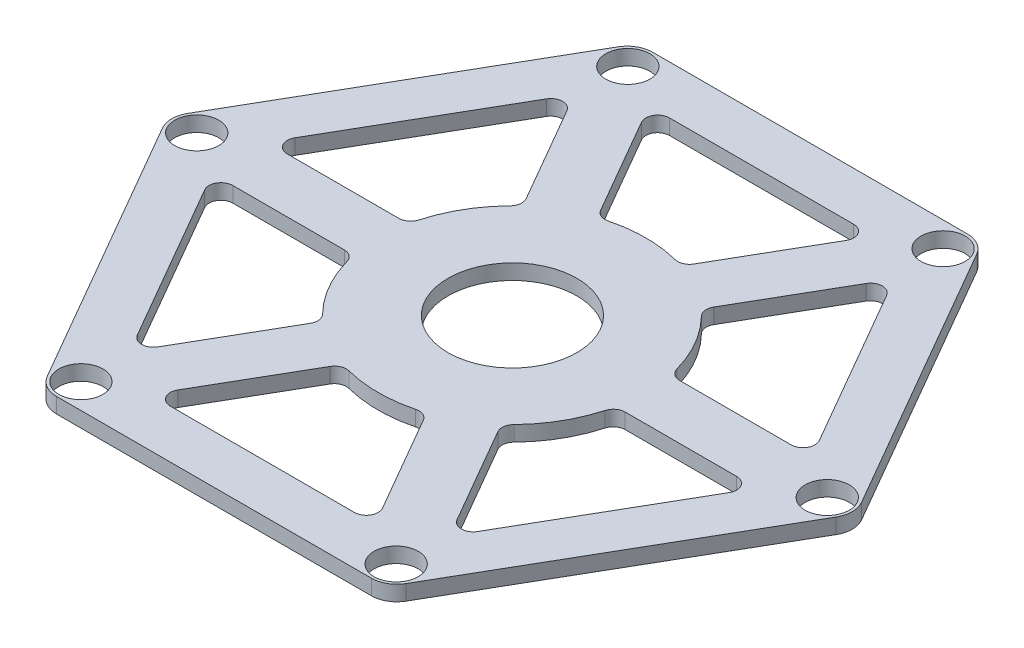
SolidWorks part; units mm, degrees
ref_plane "Front Plane" through (0, 0, 0) normal (0, 0, 1) x (1, 0, 0)
ref_plane "Top Plane" through (0, 0, 0) normal (0, 1, 0) x (1, 0, 0)
ref_plane "Right Plane" through (0, 0, 0) normal (1, 0, 0) x (0, 0, -1)
sketch "Sketch1" plane through (0, 0, 0) normal (0, 1, 0) x (1, 0, 0)
  line L1 (-20.3, 35.1606) -> (-40.6, 0)
  line L2 (-40.6, 0) -> (-20.3, -35.1606)
  line L3 (-20.3, -35.1606) -> (20.3, -35.1606)
  line L4 (20.3, -35.1606) -> (40.6, 0)
  line L5 (40.6, 0) -> (20.3, 35.1606)
  line L6 (20.3, 35.1606) -> (-20.3, 35.1606)
  line L7 (-17, 29.4449) -> (-34, 0)
  line L8 (-34, 0) -> (-17, -29.4449)
  line L9 (-17, -29.4449) -> (17, -29.4449)
  line L10 (17, -29.4449) -> (34, 0)
  line L11 (34, 0) -> (17, 29.4449)
  line L12 (17, 29.4449) -> (-17, 29.4449)
  line L13 (-18.6638, 32.2165) -> (-37.3656, -0.0563) construction
  line L14 (-37.3656, -0.0563) -> (-18.7674, -32.3889) construction
  line L15 (-18.7674, -32.3889) -> (18.5325, -32.4487) construction
  line L16 (18.5325, -32.4487) -> (37.3, 0) construction
  line L17 (37.3, 0) -> (18.6362, 32.2165) construction
  line L18 (18.6362, 32.2165) -> (-18.6638, 32.2165) construction
  line L50 (-17, 29.4449) -> (17, -29.4449) construction
  line L51 (-17, 29.4449) -> (-18.8579, 26.2268)
  line L56 (-13.2841, 29.4449) -> (-17, 29.4449)
  line L57 (-13.3543, 16.6943) -> (-7.7805, 19.9123) construction
  line L58 (-17, 29.4449) -> (-13.2841, 29.4449)
  line L59 (-13.2841, 29.4449) -> (-4.9475, 15.0054)
  line L60 (-17, 29.4449) -> (-18.8579, 26.2268)
  line L61 (-18.8579, 26.2268) -> (-10.5213, 11.7874)
  line L62 (17, 29.4449) -> (13.2841, 29.4449)
  line L63 (13.2841, 29.4449) -> (4.9475, 15.0054)
  line L66 (18.8579, 26.2268) -> (10.5213, 11.7874)
  line L67 (17, 29.4449) -> (18.8579, 26.2268)
  line L68 (34, 0) -> (32.1421, 3.2181)
  line L69 (32.1421, 3.2181) -> (15.4688, 3.2181)
  line L72 (32.1421, -3.2181) -> (15.4688, -3.2181)
  line L73 (34, 0) -> (32.1421, -3.2181)
  line L74 (17, -29.4449) -> (18.8579, -26.2268)
  line L75 (18.8579, -26.2268) -> (10.5213, -11.7874)
  line L78 (13.2841, -29.4449) -> (4.9475, -15.0054)
  line L79 (17, -29.4449) -> (13.2841, -29.4449)
  line L80 (-17, -29.4449) -> (-13.2841, -29.4449)
  line L81 (-13.2841, -29.4449) -> (-4.9475, -15.0054)
  line L84 (-18.8579, -26.2268) -> (-10.5213, -11.7874)
  line L85 (-17, -29.4449) -> (-18.8579, -26.2268)
  line L86 (-34, 0) -> (-32.1421, -3.2181)
  line L87 (-32.1421, -3.2181) -> (-15.4688, -3.2181)
  line L90 (-32.1421, 3.2181) -> (-15.4688, 3.2181)
  line L91 (-34, 0) -> (-32.1421, 3.2181)
  line L92 (18.6362, 32.2165) -> (31.4889, 27.5601) construction
  circle A0 centre (0.0529, 0) radius 7.6
  circle A2 centre (0.0529, 0) radius 11.5 construction
  arc A4 (-10.5213, 11.7874) -> (-15.4688, 3.2181) centre (0, 0) ccw
  arc A5 (4.9475, 15.0054) -> (-4.9475, 15.0054) centre (0, 0) ccw
  arc A6 (15.4688, 3.2181) -> (10.5213, 11.7874) centre (0, 0) ccw
  arc A7 (10.5213, -11.7874) -> (15.4688, -3.2181) centre (0, 0) ccw
  arc A8 (-4.9475, -15.0054) -> (4.9475, -15.0054) centre (0, 0) ccw
  arc A9 (-15.4688, -3.2181) -> (-10.5213, -11.7874) centre (0, 0) ccw
  circle A16 centre (18.6362, 32.2165) radius 2.6
  circle A17 centre (37.2184, -0.0312) radius 2.6
  circle A18 centre (18.5822, -32.2477) radius 2.6
  circle A19 centre (-18.6362, -32.2165) radius 2.6
  circle A20 centre (-37.2184, 0.0312) radius 2.6
  circle A21 centre (-18.5822, 32.2477) radius 2.6
  point P40 (0, 0)
  point P42 (0, 0)
  point P58 (0.0529, 0)
  point P59 (0, 0)
  point P62 (0, 0)
  point P77 (0, 0)
  point P82 (0, 0)
  point P92 (0, 0)
  dimension "D7" = 6
  dimension "D5" = 40
  dimension "D6" = 5.2
  dimension "D1" = 40.6
  dimension "D2" = 6.6
  dimension "D3" = 3.3
  dimension "D4" = 6
extrude "Boss-Extrude1" add sketch "Sketch1" along normal blind 1.8
fillet "Fillet1" radius 3 6 edges at (-40.6, 0.9, 0) (-20.3, 0.9, 35.1606) (20.3, 0.9, 35.1606) (40.6, 0.9, 0) (20.3, 0.9, -35.1606) (-20.3, 0.9, -35.1606)
fillet "Fillet2" radius 1.4 24 edges at (-32.1421, 0.9, 3.2181) (-15.4688, 0.9, 3.2181) (-10.5213, 0.9, 11.7874) (-18.8579, 0.9, 26.2268) (-13.2841, 0.9, 29.4449) (13.2841, 0.9, 29.4449) (-4.9475, 0.9, 15.0054) (4.9475, 0.9, 15.0054) (18.8579, 0.9, 26.2268) (10.5213, 0.9, 11.7874) (15.4688, 0.9, 3.2181) (32.1421, 0.9, 3.2181) (32.1421, 0.9, -3.2181) (18.8579, 0.9, -26.2268) (15.4688, 0.9, -3.2181) (10.5213, 0.9, -11.7874) (-32.1421, 0.9, -3.2181) (-15.4688, 0.9, -3.2181) (-4.9475, 0.9, -15.0054) (-13.2841, 0.9, -29.4449) (4.9475, 0.9, -15.0054) (13.2841, 0.9, -29.4449) (-10.5213, 0.9, -11.7874) (-18.8579, 0.9, -26.2268)
ref_plane "Plane1" through (0, 1.8, 0) normal (0, 1, 0) x (1, 0, 0)
scale "Scale1" scale about centroid uniform scaling yes scale factor 1.15
